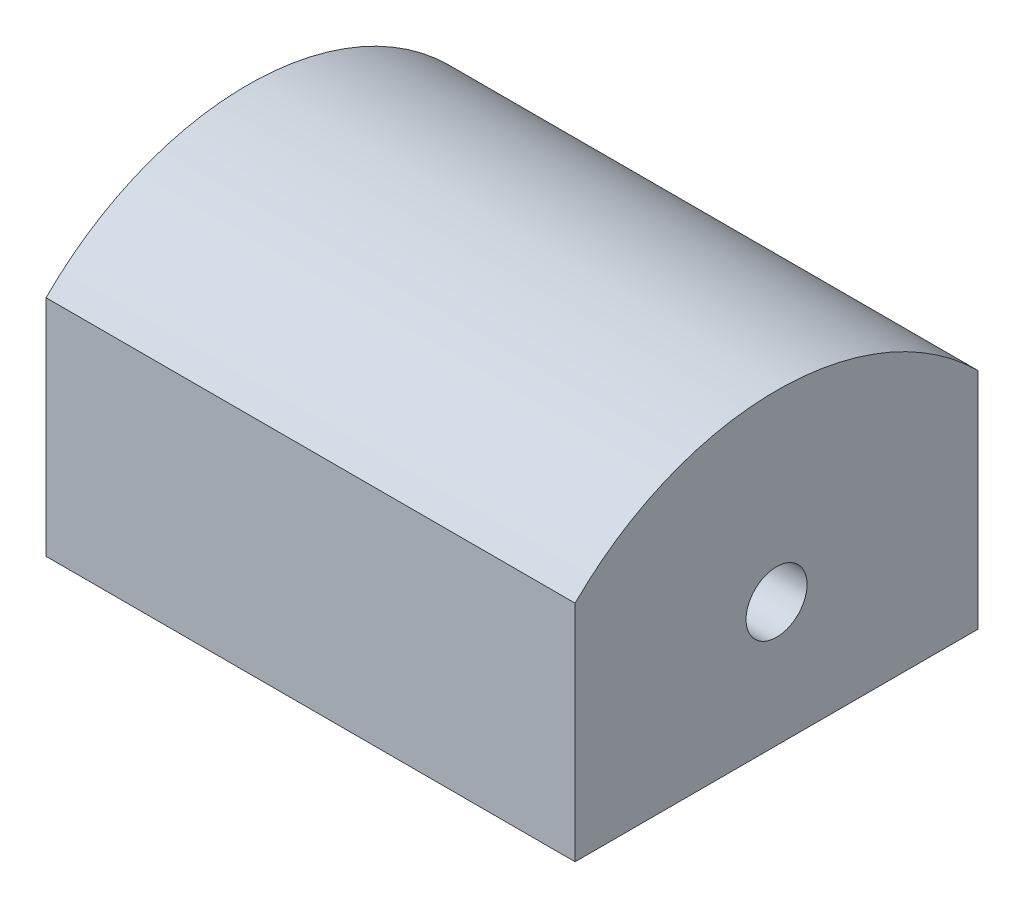
SolidWorks part; units mm, degrees
ref_plane "Front Plane" through (0, 0, 0) normal (0, 0, 1) x (1, 0, 0)
ref_plane "Top Plane" through (0, 0, 0) normal (0, 1, 0) x (1, 0, 0)
ref_plane "Right Plane" through (0, 0, 0) normal (1, 0, 0) x (0, 0, -1)
sketch "Sketch1" plane through (0, 0, 0) normal (1, 0, 0) x (0, 0, -1)
  line L0 (0, 0) -> (-9.8995, 0)
  line L1 (-9.8995, 0) -> (-9.8995, 5.5038)
  line L2 (0, 5.5038) -> (0, 0)
  arc A0 (-9.8995, 5.5038) -> (0, 5.5038) centre (-4.9497, 0.5541) cw
  dimension "D1" = 7
  dimension "D2" = 5.5038
extrude "Boss-Extrude1" add sketch "Sketch1" along normal blind 13
hole_wizard "Ø1.5mm Dowel Slot1" positions "Sketch2" profile "Sketch3" size "Ø1.5" standard "ANSI Metric" slot yes end condition through all
sketch "Sketch2" plane through (13, 0, 0) normal (1, 0, 0) x (0, 0, -1)
  arc A0 (0, 5.5038) -> (-9.8995, 5.5038) centre (-4.9497, 0.5541) ccw construction
  point P0 (-4.9497, 3.0541)
  dimension "D1" = 2.5
sketch "Sketch3" plane through (13, 3.0541, 4.9497) normal (0, 1, 0) x (0, 0, -1)
  line L0 (0, 0) -> (0, 13)
  line L1 (0, 13) -> (0.75, 13)
  line L2 (0.75, 13) -> (0.75, 0)
  line L5 (0.75, 0) -> (0, 0)
  line L11 (0, -6.35) -> (0, 107.95) construction
  dimension "Thru Hole Dia." = 1.5
  dimension "Thru Hole Depth" = 13
